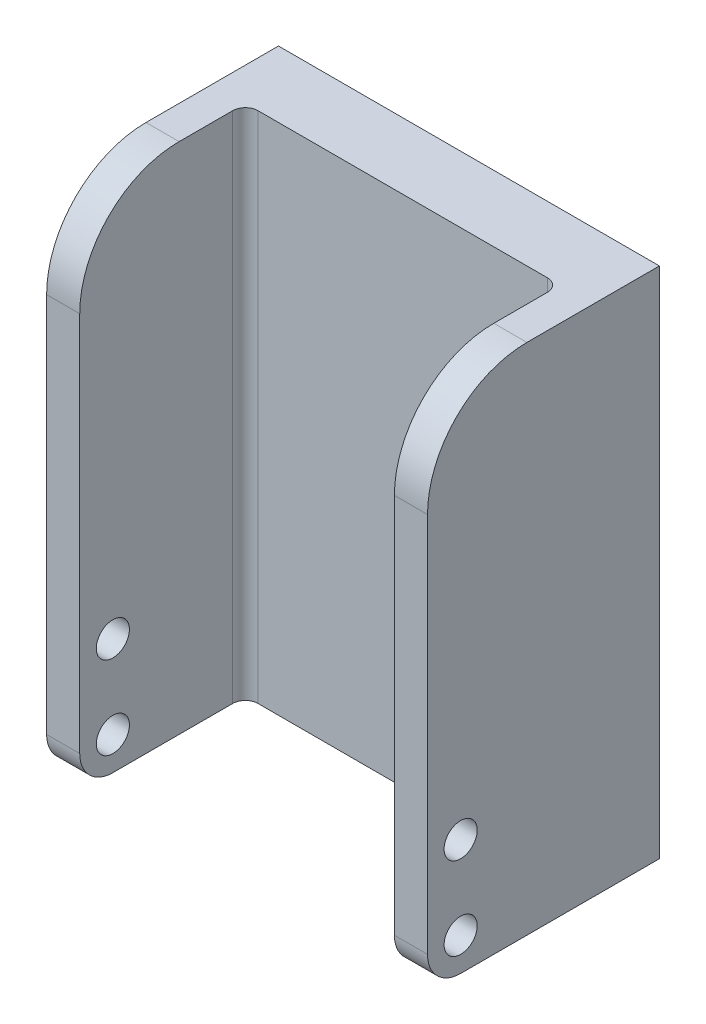
SolidWorks part; units mm, degrees
ref_plane "Front Plane" through (0, 0, 0) normal (0, 0, 1) x (1, 0, 0)
ref_plane "Top Plane" through (0, 0, 0) normal (0, 1, 0) x (1, 0, 0)
ref_plane "Right Plane" through (0, 0, 0) normal (1, 0, 0) x (0, 0, -1)
sketch "Sketch1" plane through (0, 0, 0) normal (0, 0, 1) x (1, 0, 0)
  line L1 (-11.5, -15.5) -> (11.5, -15.5)
  line L2 (-11.5, -15.5) -> (-11.5, 15.5)
  line L3 (-11.5, 15.5) -> (11.5, 15.5)
  line L4 (11.5, -15.5) -> (11.5, 15.5)
  line L5 (-11.5, -15.5) -> (11.5, 15.5) construction
  line L6 (-11.5, 15.5) -> (11.5, -15.5) construction
  point P0 (0, 0)
  dimension "D1" = 23
  dimension "D2" = 31
extrude "Boss-Extrude1" add sketch "Sketch1" along normal blind 4
sketch "Sketch2" plane through (11.5, 0, 0) normal (1, 0, 0) x (0, 0, -1)
  line L0 (-4, 15.5) -> (-14, 15.5)
  line L1 (-14, 15.5) -> (-14, -15.5)
  line L2 (-14, -15.5) -> (-4, -15.5)
  line L3 (-4, -15.5) -> (0, -15.5) construction
  line L4 (-4, -15.5) -> (-4, 15.5) construction
  line L5 (-4, -15.5) -> (-4, 15.5)
  dimension "D1" = 10
extrude "Boss-Extrude2" add sketch "Sketch2" against normal blind 2
mirror "Mirror1" about plane through (0, 0, 0) normal (1, 0, 0) of "Boss-Extrude2"
sketch "Sketch3" plane through (11.5, 0, 0) normal (1, 0, 0) x (0, 0, -1)
  line L0 (-14, 15.5) -> (-14, -15.5) construction
  line L1 (-14, -15.5) -> (0, -15.5) construction
  circle A0 centre (-12, -13.5) radius 1
  circle A1 centre (-12, -13.5) radius 1
  circle A2 centre (-12, -8.5) radius 1
  dimension "D1" = 2
  dimension "D2" = 2
  dimension "D3" = 2
  dimension "D4" = 0
  dimension "D5" = 5
extrude "Cut-Extrude1" cut sketch "Sketch3" against normal through all contours A2 | A0
fillet "Fillet1" radius 2 2 edges at (-10.5, -15.5, 14) (10.5, -15.5, 14)
fillet "Fillet2" radius 6 2 edges at (-10.5, 15.5, 14) (10.5, 15.5, 14)
fillet "Fillet3" radius 0.762 2 edges at (-9.5, 0, 4) (9.5, 0, 4)
